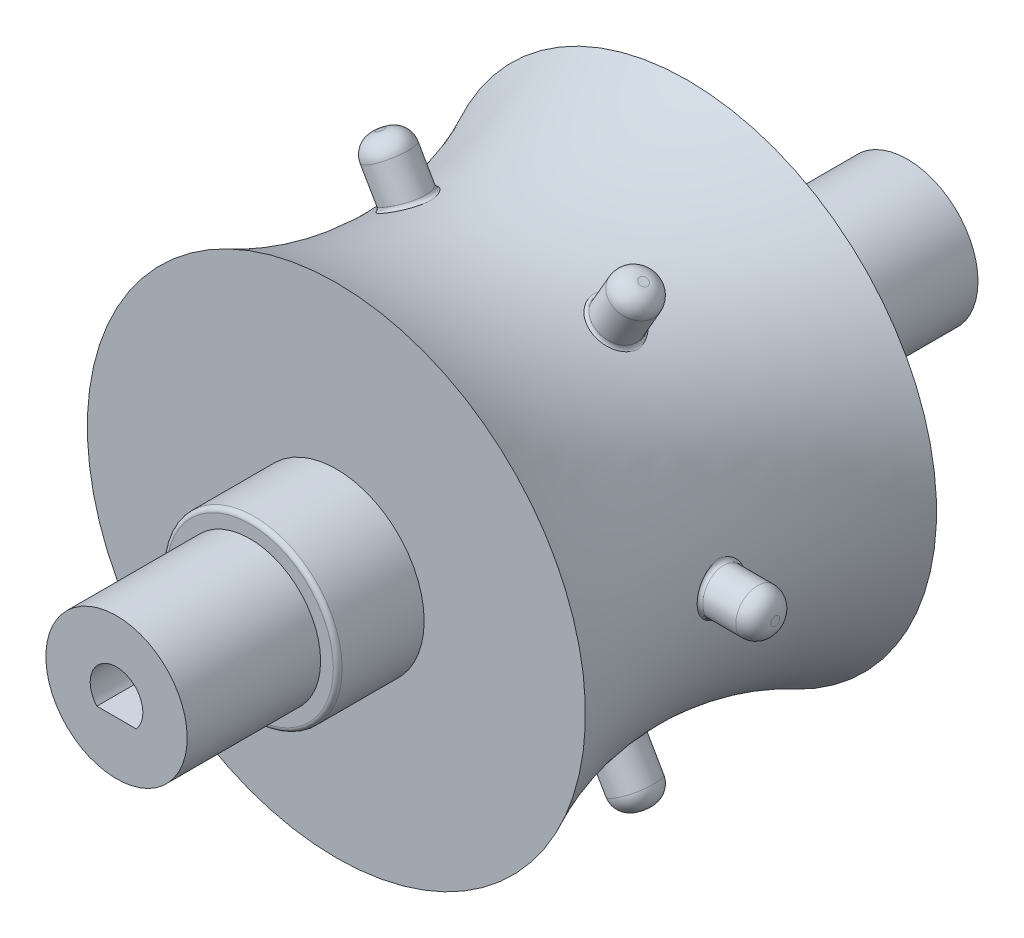
SolidWorks part; units mm, degrees
ref_plane "Front Plane" through (0, 0, 0) normal (0, 0, 1) x (1, 0, 0)
ref_plane "Top Plane" through (0, 0, 0) normal (0, 1, 0) x (1, 0, 0)
ref_plane "Right Plane" through (0, 0, 0) normal (1, 0, 0) x (0, 0, -1)
sketch "Sketch1" plane through (0, 0, 0) normal (0, 0, 1) x (1, 0, 0)
  circle A0 centre (0, 0) radius 4.025
  dimension "D1" = 8.05
extrude "Boss-Extrude1" add sketch "Sketch1" along normal blind 45.05
sketch "Sketch2" plane through (0, 0, 45.05) normal (0, 0, 1) x (1, 0, 0)
  line L2 (-1.2196, -1.1113) -> (1.2196, -1.1113)
  arc A5 (-1.2196, -1.1113) -> (1.2196, -1.1113) centre (0, 0) cw
  circle A6 centre (0, 0) radius 4.025 construction
  dimension "D1" = 1.65
  dimension "D2" = 1.2196
extrude "Cut-Extrude1" [suppressed] cut sketch "Sketch2" against normal blind 9
sketch "Sketch3" plane through (0, 0, 0) normal (1, 0, 0) x (0, 0, -1)
  line L0 (0, 0) -> (-45.05, 0) construction
  line L1 (-45.05, 4.025) -> (-45.05, -4.025) construction
  circle A0 centre (-22.525, 0) radius 1.25
  dimension "D1" = 2.5
extrude "Boss-Extrude2" add sketch "Sketch3" along normal blind 15
fillet "Fillet1" radius 1 1 edges at (15, 0, 21.275)
pattern_circular "CirPattern1" count 6 over 360 about axis through (0, 0, 0) along (0, 0, 1) of "Boss-Extrude2", "Fillet1"
fillet "Fillet2" radius 1 6 edges at (-0.851, -3.934, 22.7478) (-4.0189, -0.222, 21.2949) (-2.9814, 2.704, 22.7478) (0.851, -3.934, 22.3022) (0.851, 3.934, 22.7478) (4.0189, 0.222, 21.2949)
ref_plane "Plane1" through (0, 0, 37.45) normal (0, 0, 1) x (1, 0, 0)
ref_plane "Plane2" through (0, 0, 7.6) normal (0, 0, -1) x (-1, 0, 0)
sketch "Sketch4" plane through (0, 0, 37.45) normal (0, 0, 1) x (1, 0, 0)
  circle A0 centre (0, 0) radius 5
  dimension "D1" = 10
extrude "Boss-Extrude3" [suppressed] add sketch "Sketch4" against normal blind 1.25
sketch "Sketch5" plane through (0, 0, 7.6) normal (0, 0, -1) x (-1, 0, 0)
  circle A0 centre (0, 0) radius 5
  dimension "D1" = 10
extrude "Boss-Extrude4" add sketch "Sketch5" against normal up to surface (29.85 mm away) up to plane "Plane1"
fillet "Fillet4" radius 0.25 2 edges at (5, 0, 37.45) (-5, 0, 7.6)
sketch "Sketch6" plane through (0, 0, 0) normal (0, 0, -1) x (-1, 0, 0)
  line L0 (-1.12, -0.9978) -> (1.12, -0.9978)
  arc A0 (-1.12, -0.9978) -> (1.12, -0.9978) centre (0, 0) cw
  circle A1 centre (0, 0) radius 4.025 construction
  dimension "D1" = 1.5
  dimension "D2" = 1.12
extrude "Cut-Extrude2" cut sketch "Sketch6" against normal blind 10
sketch "Sketch9" plane through (0, 0, 0) normal (1, 0, 0) x (0, 0, -1)
  line L0 (0, 0) -> (-45.05, 0) construction
  line L1 (-45.05, 4.025) -> (-45.05, -4.025) construction
  line L2 (-22.525, 22.69) -> (-22.525, -22.69) construction
  point P8 (-22.525, 0)
ref_plane "Plane3" through (0, 0, 22.525) normal (0, 0, 1) x (1, 0, 0)
sketch "Sketch12" plane through (0, 0, 22.525) normal (0, 0, 1) x (1, 0, 0)
  circle A0 centre (0, 0) radius 11.875
  dimension "D1" = 23.75
extrude "Boss-Extrude5" add sketch "Sketch12" along normal mid plane 20
fillet "Fillet5" radius 0.25 8 edges at (-11.8717, -0.2797, 23.7433) (4.8511, 10.8389, 22.2453) (4.8511, -10.8389, 22.8047) (-4.8511, -10.8389, 22.2453) (-6.9612, 9.6206, 22.2453) (11.8717, -0.2797, 21.3067) (11.875, 0, 12.525) (11.875, 0, 32.525)
sketch "Sketch14" plane through (0, 0, 22.525) normal (0, 0, 1) x (1, 0, 0)
  circle A0 centre (0, 0) radius 25
extrude "Cut-Extrude3" [suppressed] cut sketch "Sketch14" against normal through all
ref_plane "Plane4" through (0, 0, 0) normal (0, 1, 0) x (1, 0, 0)
sketch "Sketch16" plane through (0, 0, 0) normal (0, 1, 0) x (1, 0, 0)
  line L3 (0, -12.525) -> (0, -32.525)
  line L4 (0, -32.525) -> (14.1884, -32.525)
  line L5 (14.1884, -12.525) -> (0, -12.525)
  line L6 (11.625, -12.525) -> (-11.625, -12.525) construction
  line L7 (-11.625, -32.525) -> (11.625, -32.525) construction
  line L8 (0, 0) -> (0, -45.05) construction
  line L9 (11.875, -21.025) -> (11.875, -12.775) construction
  arc A0 (14.1884, -12.525) -> (14.1884, -32.525) centre (34.645, -22.525) ccw
  dimension "D1" = 22.77
revolve "Revolve1" add sketch "Sketch16" angle 360 about L0
sketch "Sketch17" plane through (0, 0, 45.05) normal (0, 0, 1) x (1, 0, 0)
  line L1 (-1.12, -0.9978) -> (1.12, -0.9978)
  line L2 (-1.12, -0.9978) -> (1.12, -0.9978)
  arc A1 (1.12, -0.9978) -> (-1.12, -0.9978) centre (0, 0) ccw
  arc A2 (1.12, -0.9978) -> (-1.12, -0.9978) centre (0, 0) ccw
  dimension "D1" = 0
extrude "Cut-Extrude4" cut sketch "Sketch17" against normal blind 10
